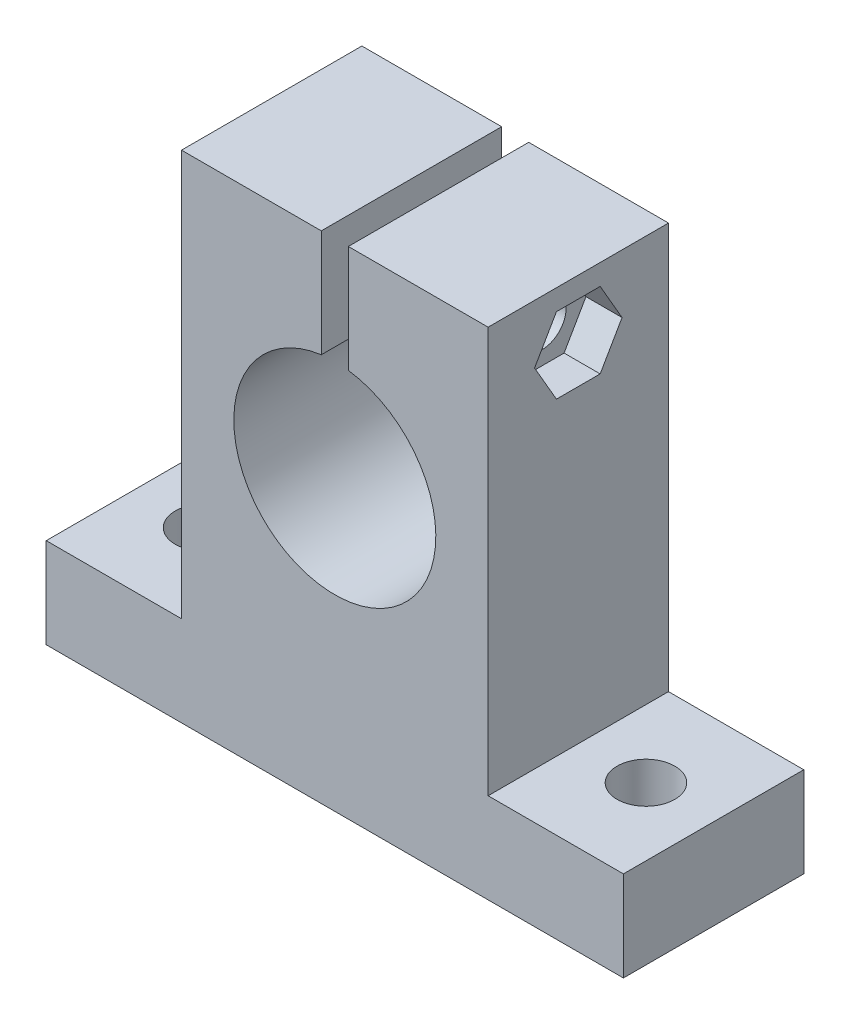
SolidWorks part; units mm, degrees
ref_plane "前视基准面" through (0, 0, 0) normal (0, 0, 1) x (1, 0, 0)
ref_plane "上视基准面" through (0, 0, 0) normal (0, 1, 0) x (1, 0, 0)
ref_plane "右视基准面" through (0, 0, 0) normal (1, 0, 0) x (0, 0, -1)
sketch "草图1" plane through (0, 0, 0) normal (0, 0, 1) x (1, 0, 0)
  line L0 (0, 84.321) -> (0, -94.6914) construction
  line L1 (-87.1605, 0) -> (139.0123, 0) construction
  line L2 (17, -0.1975) -> (1.5, -0.1975)
  line L3 (17, -0.1975) -> (17, -45.1975)
  line L5 (-17, -0.1975) -> (-17, -45.1975)
  line L7 (-32, -55.1975) -> (32, -55.1975)
  line L8 (-32, -55.1975) -> (-32, -45.1975)
  line L9 (-32, -45.1975) -> (-17, -45.1975)
  line L10 (32, -55.1975) -> (32, -45.1975)
  line L11 (17, -45.1975) -> (32, -45.1975)
  line L12 (-1.5, -0.1975) -> (-1.5, -12.0984)
  line L13 (1.5, -0.1975) -> (1.5, -12.0984)
  line L14 (-1.5, -0.1975) -> (-17, -0.1975)
  arc A0 (-1.5, -12.0984) -> (1.5, -12.0984) centre (0, -23.1975) ccw
  point P19 (0, 0)
  dimension "D5" = 22.4
  dimension "D1" = 10
  dimension "D2" = 64
  dimension "D3" = 34
  dimension "D4" = 55
  dimension "D6" = 32
  dimension "D7" = 1.5
extrude "凸台-拉伸1" add sketch "草图1" along normal blind 20
sketch "草图2" plane through (0, 0, 0) normal (1, 0, 0) x (0, 0, -1)
  line L0 (-10, 16.0659) -> (-10, -70.2183) construction
  line L1 (-20, -45.1975) -> (-20, -0.1975) construction
  line L2 (0, -45.1975) -> (0, -0.1975) construction
  line L3 (-20, -0.1975) -> (0, -0.1975) construction
  circle A0 centre (-10, -6.6975) radius 2.65
  dimension "D1" = 5.3
  dimension "D2" = 6.5
extrude "切除-拉伸1" cut sketch "草图2" against normal mid plane 40
sketch "草图3" plane through (17, 0, 0) normal (1, 0, 0) x (0, 0, -1)
  line L0 (-20, -0.1975) -> (0, -0.1975) construction
  line L1 (-5.1508, -6.6975) -> (-7.5754, -2.498)
  line L2 (-7.5754, -2.498) -> (-12.4246, -2.498)
  line L3 (-12.4246, -2.498) -> (-14.8492, -6.6975)
  line L4 (-14.8492, -6.6975) -> (-12.4246, -10.8971)
  line L5 (-12.4246, -10.8971) -> (-7.5754, -10.8971)
  line L6 (-7.5754, -10.8971) -> (-5.1508, -6.6975)
  circle A0 centre (-10, -6.6975) radius 4.1996 construction
  dimension "D1" = 8.3991
extrude "切除-拉伸2" cut sketch "草图3" against normal blind 4
sketch "草图5" plane through (0, -55.1975, 0) normal (0, -1, 0) x (1, 0, 0)
  line L0 (-44.0709, 10) -> (42.8573, 10) construction
  line L1 (-32, 20) -> (32, 20) construction
  line L2 (-32, 0) -> (32, 0) construction
  line L3 (0, 30.7578) -> (0, -10.375) construction
  line L4 (32, 20) -> (32, 0) construction
  line L5 (-32, 20) -> (-32, 0) construction
  circle A0 centre (-24.5, 10) radius 3.2
  circle A1 centre (24.5, 10) radius 3.2
  dimension "D1" = 6.4
  dimension "D2" = 49
extrude "切除-拉伸3" cut sketch "草图5" against normal through all
